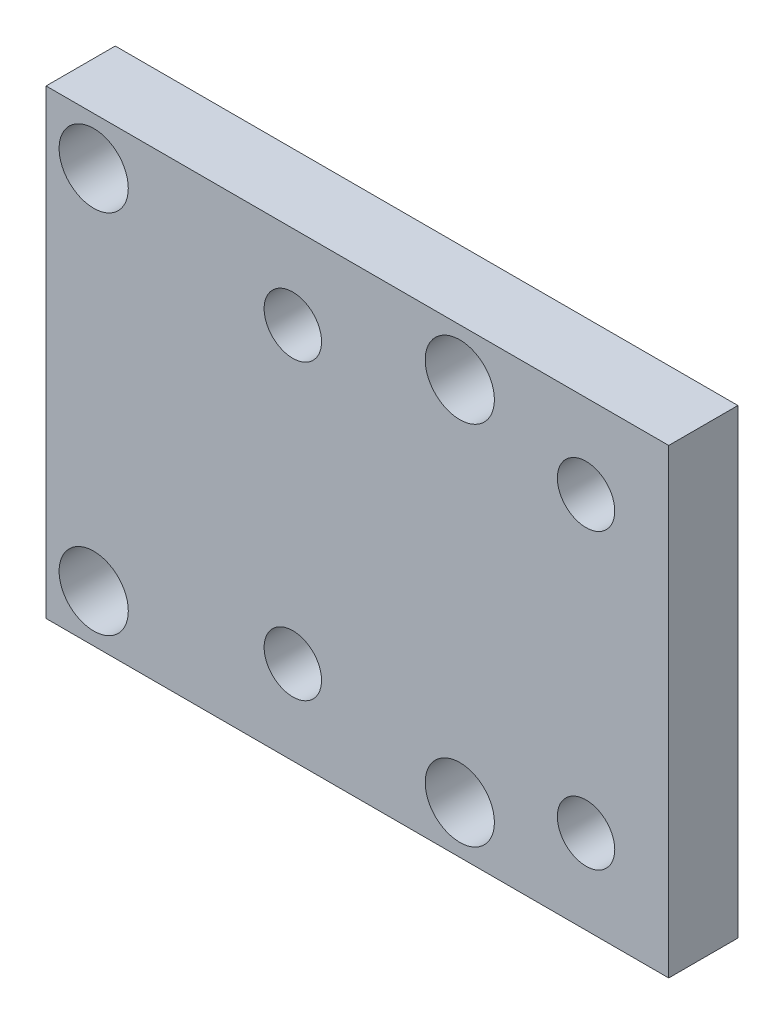
SolidWorks part; units mm, degrees
ref_plane "Front Plane" through (0, 0, 0) normal (0, 0, 1) x (1, 0, 0)
ref_plane "Top Plane" through (0, 0, 0) normal (0, 1, 0) x (1, 0, 0)
ref_plane "Right Plane" through (0, 0, 0) normal (1, 0, 0) x (0, 0, -1)
sketch "Sketch1" plane through (0, 0, 0) normal (0, 0, 1) x (1, 0, 0)
  line L1 (-11.43, 0) -> (-65.43, 0)
  line L2 (-11.43, 0) -> (-11.43, -40)
  line L3 (-11.43, -40) -> (-65.43, -40)
  line L4 (-65.43, 0) -> (-65.43, -40)
  dimension "D1" = 54
  dimension "D2" = 40
extrude "Boss-Extrude1" add sketch "Sketch1" along normal blind 6
sketch "Sketch2" plane through (0, 0, 0) normal (0, 0, 1) x (1, 0, 0)
  line L4 (-65.43, 0) -> (-65.43, -40) construction
  line L6 (-65.43, -40) -> (-11.43, -40) construction
  circle A6 centre (-61.3, -35.875) radius 2
  circle A7 centre (-29.55, -35.875) radius 2
  circle A8 centre (-29.55, -4.125) radius 2
  circle A9 centre (-61.3, -4.125) radius 2
  dimension "D1" = 31.75
  dimension "D2" = 31.75
  dimension "D3" = 4.13
  dimension "D4" = 4
  dimension "D5" = 4.125
  dimension "D6" = 2
  dimension "D7" = 2
extrude "Cut-Extrude2" cut sketch "Sketch2" along normal through all
sketch "Sketch8" plane through (0, 0, 6) normal (0, 0, 1) x (1, 0, 0)
  circle A0 centre (-61.3, -4.125) radius 3
  circle A3 centre (-29.55, -4.125) radius 3
  circle A4 centre (-29.55, -35.875) radius 3
  circle A5 centre (-61.3, -35.875) radius 3
  dimension "D1" = 6
  dimension "D2" = 2
  dimension "D3" = 2
extrude "Cut-Extrude6" cut sketch "Sketch8" against normal blind 5
sketch "Sketch9" plane through (0, 0, 6) normal (0, 0, 1) x (1, 0, 0)
  line L0 (-18.6008, -7.27) -> (-18.6008, -43.6541) construction
  line L1 (-18.6008, -7.27) -> (-44.0308, -7.27) construction
  line L2 (-44.0308, -7.27) -> (-44.0308, -32.7) construction
  line L3 (-44.0308, -32.7) -> (-18.6008, -32.7) construction
  circle A0 centre (-44.0308, -7.27) radius 2.49
  circle A1 centre (-18.6008, -7.27) radius 2.49
  circle A2 centre (-44.0308, -32.7) radius 2.49
  circle A3 centre (-18.6008, -32.7) radius 2.49
  dimension "D2" = 25.43
  dimension "D3" = 25.43
  dimension "D4" = 2
  dimension "D5" = 2
extrude "Cut-Extrude7" cut sketch "Sketch9" against normal up to surface (6 mm away) up to face at (-27.55, -4.125, 0)
equation "\"hole_screw_1_4_20\"= 6"
equation "\"inch\"=25.43"
